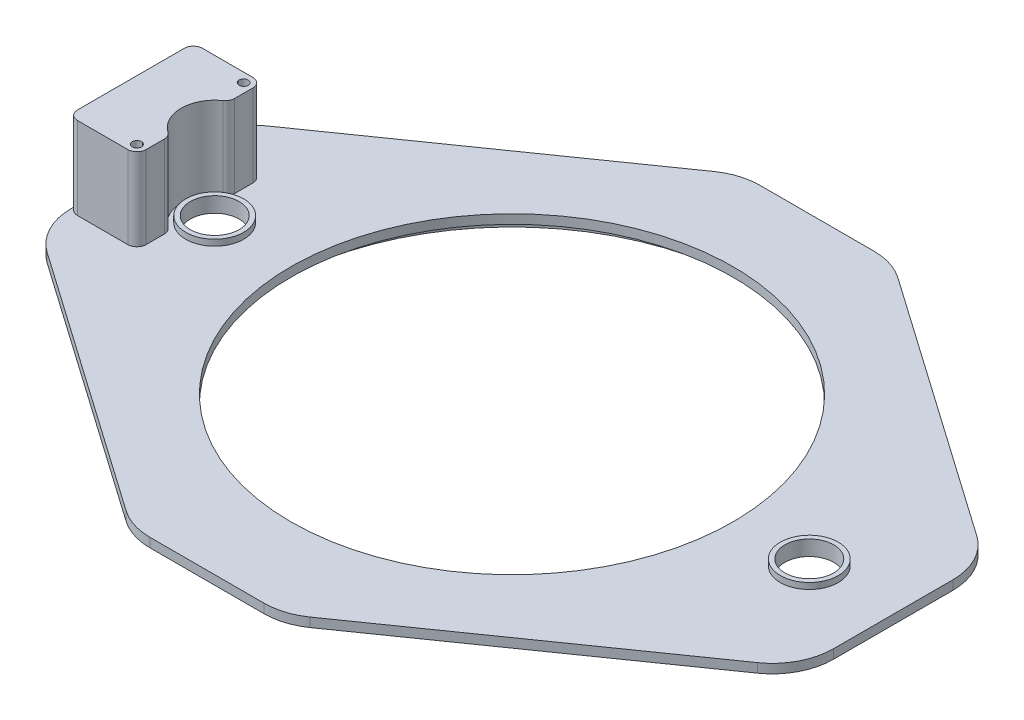
SolidWorks part; units mm, degrees
ref_plane "Front" through (0, 0, 0) normal (0, 0, 1) x (1, 0, 0)
ref_plane "Top" through (0, 0, 0) normal (0, 1, 0) x (1, 0, 0)
ref_plane "Right" through (0, 0, 0) normal (1, 0, 0) x (0, 0, -1)
sketch "Sketch1" plane through (0, 0, 0) normal (0, 1, 0) x (1, 0, 0)
  line L1 (-115, -100) -> (115, -100)
  line L2 (-125, -90) -> (-125, 90)
  line L3 (-115, 100) -> (115, 100)
  line L4 (125, -90) -> (125, 90)
  line L5 (-125, -100) -> (125, 100) construction
  line L6 (-125, 100) -> (125, -100) construction
  circle A0 centre (0, 0) radius 77.5 construction
  arc A1 (-115, -100) -> (-125, -90) centre (-115, -90) cw
  arc A2 (115, -100) -> (125, -90) centre (115, -90) ccw
  arc A3 (115, 100) -> (125, 90) centre (115, 90) cw
  arc A4 (-125, 90) -> (-115, 100) centre (-115, 90) cw
  point P0 (0, 0)
  dimension "D1" = 155
  dimension "D4" = 10
  dimension "D2" = 250
  dimension "D3" = 200
extrude "Boss-Extrude1" add sketch "Sketch1" along normal blind 3
sketch "Sketch2" plane through (0, 3, 0) normal (0, 1, 0) x (1, 0, 0)
  circle A0 centre (-97.5, 0) radius 8
  dimension "D2" = 16
  dimension "D1" = 97.5
extrude "Cut-Extrude1" cut sketch "Sketch2" against normal through all
mirror "Mirror1" about plane through (0, 0, 0) normal (1, 0, 0) of "Cut-Extrude1"
sketch "Sketch4" plane through (0, 0, 0) normal (0, 1, 0) x (1, 0, 0)
  circle A0 centre (0, 0) radius 78.5
  dimension "D1" = 157
sketch "Sketch5" plane through (0, 0, 0) normal (0, 1, 0) x (1, 0, 0)
  circle A0 centre (0, 0) radius 72.5
  dimension "D1" = 145
extrude "Cut-Extrude4" cut sketch "Sketch5" along normal through all
extrude "Extrude-Thin1" add sketch "Sketch4" against normal blind 5 thin
sketch "Sketch6" plane through (0, 3, 0) normal (0, 1, 0) x (1, 0, 0)
  line L0 (-125, 90) -> (-125, -90) construction
  line L1 (-105.5, 17.5) -> (-105.5, -17.5) construction
  line L3 (-122, -20.5) -> (-105.5, -20.5)
  line L4 (-125, -17.5) -> (-125, 17.5)
  line L5 (-122, 20.5) -> (-105.5, 20.5)
  line L6 (-102.5, -17.5) -> (-102.5, 17.5)
  line L7 (-125, -20.5) -> (-102.5, 20.5) construction
  line L8 (-125, 20.5) -> (-102.5, -20.5) construction
  circle A0 centre (-105.5, 17.5) radius 1.5
  circle A1 centre (-105.5, -17.5) radius 1.5
  circle A2 centre (-97.5, 0) radius 8 construction
  circle A3 centre (-97.5, 0) radius 8 construction
  arc A4 (-125, 17.5) -> (-122, 20.5) centre (-122, 17.5) cw
  arc A5 (-105.5, 20.5) -> (-102.5, 17.5) centre (-105.5, 17.5) cw
  arc A6 (-122, -20.5) -> (-125, -17.5) centre (-122, -17.5) cw
  arc A7 (-105.5, -20.5) -> (-102.5, -17.5) centre (-105.5, -17.5) ccw
  circle A8 centre (-97.5, 0) radius 11
  point P4 (-105.5, 0)
  point P7 (-113.75, 0)
  point P13 (-125, 0)
  circle M6 centre (-97.5, 0) radius 8
  line M14 (-125, 90) -> (-125, -90)
  dimension "D3" = 3
  dimension "D6" = 3
  dimension "D7" = 22
  dimension "D1" = 19.5
  dimension "D2" = 35
  dimension "D4" = 3
  dimension "D5" = 3
extrude "Boss-Extrude2" add sketch "Sketch6" along normal blind 27 contours L3 A7 L6 A5 L5 A4 A6 A0 A1 M6 M14
fillet "Fillet1" radius 3 2 edges at (-102.5, 16.5, -9.798) (-102.5, 16.5, 9.798)
sketch "Sketch7" plane through (0, 3, 0) normal (0, 1, 0) x (1, 0, 0)
  line L1 (125, -90) -> (125, 90) construction
  line L2 (-125, -100) -> (125, -100)
  line L3 (-125, -100) -> (-125, 100)
  line L4 (-125, 100) -> (125, 100)
  line L5 (125, -100) -> (125, 100)
  line L6 (-125, -100) -> (125, 100) construction
  line L7 (-125, 100) -> (125, -100) construction
  line L8 (-115, -100) -> (115, -100) construction
  line L9 (-125, 30) -> (-25, 100)
  line L10 (25, 100) -> (125, 30)
  line L11 (125, -30) -> (25, -100)
  line L12 (-125, -30) -> (-25, -100)
  point P0 (0, 0)
  arc M34 (-125, -90) -> (-115, -100) centre (-115, -90) ccw
  line M35 (-115, -100) -> (115, -100)
  arc M36 (115, -100) -> (125, -90) centre (115, -90) ccw
  line M37 (125, -90) -> (125, 90)
  arc M38 (125, 90) -> (115, 100) centre (115, 90) ccw
  line M39 (115, 100) -> (-115, 100)
  arc M40 (-115, 100) -> (-125, 90) centre (-115, 90) ccw
  line M41 (-125, 90) -> (-125, 17.5)
  dimension "D1" = 100
  dimension "D2" = 70
  dimension "D3" = 70
  dimension "D4" = 70
  dimension "D5" = 70
extrude "Cut-Extrude5" cut sketch "Sketch7" against normal blind 10 contours L9 L4 M41 M40 | L10 L5 M39 M38 | L11 L2 M37 M36 | L12 L3 M34 M35
fillet "Fillet2" radius 20 8 edges at (-125, 1.5, -30) (-125, 1.5, 30) (-25, 1.5, 100) (25, 1.5, 100) (125, 1.5, 30) (125, 1.5, -30) (25, 1.5, -100) (-25, 1.5, -100)
sketch "Sketch8" plane through (0, 3, 0) normal (0, 1, 0) x (1, 0, 0)
  circle A0 centre (-97.5, 0) radius 8 construction
  circle A1 centre (97.5, 0) radius 8 construction
  circle A2 centre (-97.5, 0) radius 8
  circle A3 centre (97.5, 0) radius 8
extrude "Extrude-Thin2" add sketch "Sketch8" along normal blind 2 thin
equation "\"Kova_d\"= 155mm"
equation "\"Kova_h\"= 100mm"
equation "\"D1@Sketch1\"=\"Kova_d\""
equation "\"Plaka_h\"= 200mm"
equation "\"D2@Sketch1\"=\"Plaka_L\""
equation "\"D3@Sketch1\"=\"Plaka_h\""
equation "\"Plaka_L\"= 250mm"
equation "\"D1@Sketch2\"= \"Kova_d\" / 2 + 20"
equation "\"Saplama_d\"= 5mm"
equation "\"D1@Sketch4\"=\"Kova_d\"+2"
equation "\"D1@Sketch5\"=\"Kova_d\"-10"
equation "\"D3@Sketch7\"=\"D2@Sketch7\""
equation "\"D4@Sketch7\"=\"D2@Sketch7\""
equation "\"D5@Sketch7\"=\"D2@Sketch7\""
